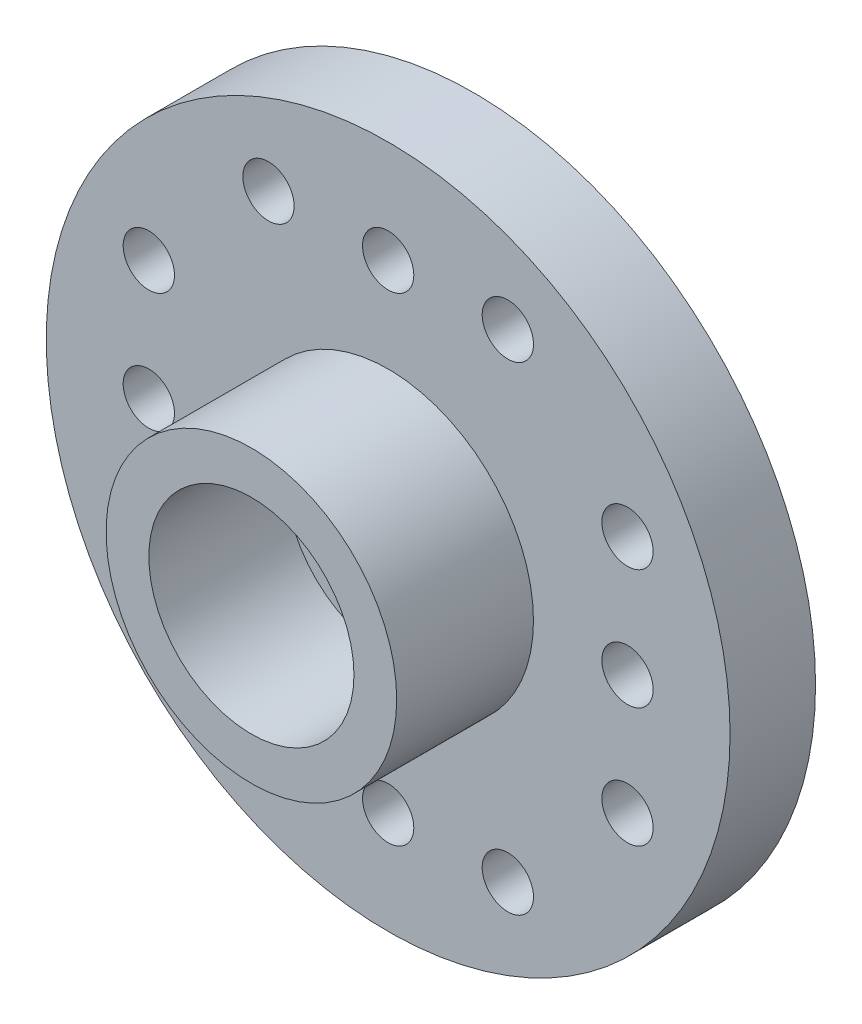
SolidWorks part; units mm, degrees
ref_plane "Front Plane" through (0, 0, 0) normal (0, 0, 1) x (1, 0, 0)
ref_plane "Top Plane" through (0, 0, 0) normal (0, 1, 0) x (1, 0, 0)
ref_plane "Right Plane" through (0, 0, 0) normal (1, 0, 0) x (0, 0, -1)
sketch "Sketch1" plane through (0, 0, 0) normal (0, 0, 1) x (1, 0, 0)
  line L0 (-7, 3.5) -> (-7, -3.5) construction
  line L1 (-7, 0) -> (0, 0) construction
  circle A0 centre (0, 0) radius 10
  circle A1 centre (-7, 0) radius 0.75
  circle A2 centre (3.5, 7) radius 0.75
  circle A3 centre (0, 7) radius 0.75
  circle A4 centre (-3.5, 7) radius 0.75
  circle A5 centre (7, -3.5) radius 0.75
  circle A6 centre (7, 0) radius 0.75
  circle A7 centre (7, 3.5) radius 0.75
  circle A8 centre (-3.5, -7) radius 0.75
  circle A9 centre (0, -7) radius 0.75
  circle A10 centre (3.5, -7) radius 0.75
  circle A11 centre (-7, -3.5) radius 0.75
  circle A13 centre (-7, 3.5) radius 0.75
  circle A22 centre (0, 0) radius 1.5
  point P25 (0, 0)
  dimension "D2" = 20
  dimension "D4" = 7
  dimension "D5" = 3.5
  dimension "D14" = 3
  dimension "D6" = 3.5
  dimension "D3" = 1.5
extrude "Boss-Extrude1" add sketch "Sketch1" along normal blind 2.5
sketch "Sketch5" plane through (0, 0, 2.5) normal (0, 0, 1) x (1, 0, 0)
  circle A0 centre (0, 0) radius 3
  circle A1 centre (0, 0) radius 4.25
  dimension "D1" = 8.5
  dimension "D2" = 6
extrude "Boss-Extrude2" add sketch "Sketch5" along normal blind 4
